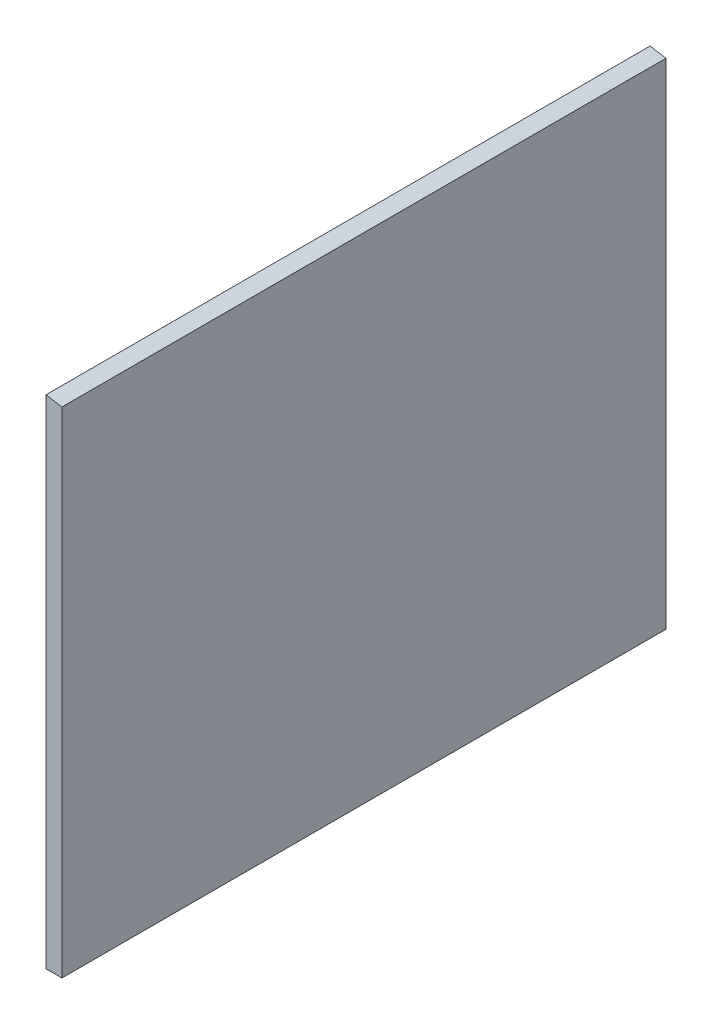
SolidWorks part; units mm, degrees
ref_plane "Front Plane" through (0, 0, 0) normal (0, 0, 1) x (1, 0, 0)
ref_plane "Top Plane" through (0, 0, 0) normal (0, 1, 0) x (1, 0, 0)
ref_plane "Right Plane" through (0, 0, 0) normal (1, 0, 0) x (0, 0, -1)
sketch "Sketch1" plane through (0, 0, 0) normal (0, 0, 1) x (1, 0, 0)
  line L0 (0, 0) -> (0, 93.98)
  line L6 (0, 93.98) -> (3, 93.4704)
  line L7 (3, 93.4704) -> (3, 0)
  line L8 (3, 0) -> (0, 0)
  dimension "D1" = 80.36
  dimension "D3" = 3
  dimension "D4" = 93.98
extrude "Boss-Extrude1" add sketch "Sketch1" along normal mid plane 114.188
